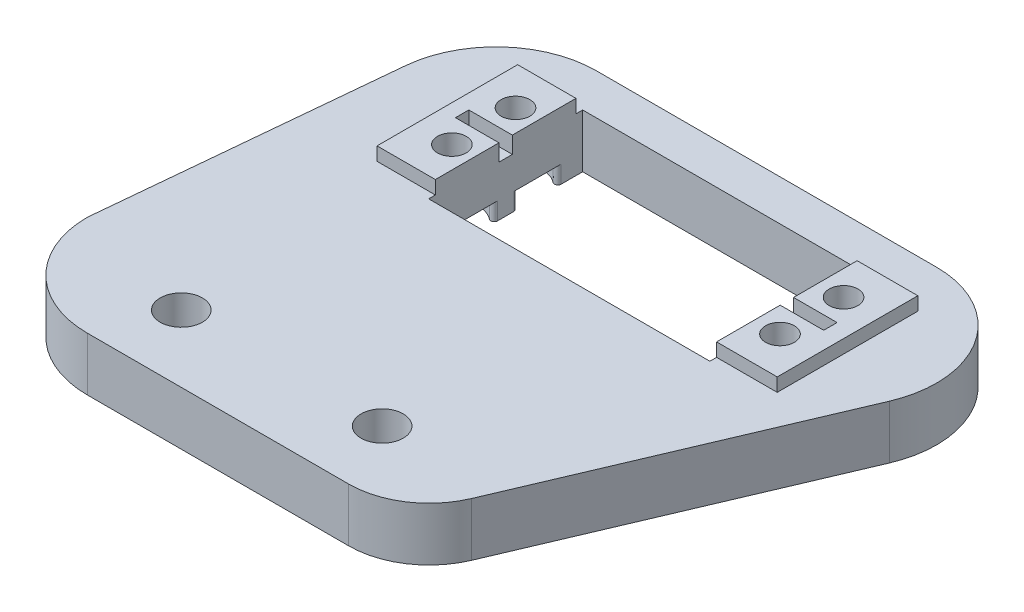
SolidWorks part; units mm, degrees
ref_plane "Front Plane" through (0, 0, 0) normal (0, 0, 1) x (1, 0, 0)
ref_plane "Top Plane" through (0, 0, 0) normal (0, 1, 0) x (1, 0, 0)
ref_plane "Right Plane" through (0, 0, 0) normal (1, 0, 0) x (0, 0, -1)
sketch "Sketch1" plane through (0, 0, 0) normal (0, 1, 0) x (1, 0, 0)
  line L8 (25.9808, 0) -> (65.0096, 0)
  line L9 (10.9808, 15) -> (14.0144, 46.6718)
  line L11 (76.0535, 7.306) -> (90.6678, 41.6903)
  line L12 (90.6678, 41.6903) -> (92.1063, 45.0748)
  line L16 (14.0144, 46.6718) -> (15.1359, 58.3798)
  line L17 (92.1063, 45.0748) -> (94.6596, 51.0821)
  line L19 (80.8548, 71.9495) -> (30.0676, 71.9495)
  arc A7 (25.9808, 0) -> (10.9808, 15) centre (25.9808, 15) cw
  arc A11 (76.0535, 7.306) -> (65.0096, 0) centre (65.0096, 12) cw
  arc A14 (80.8548, 71.9495) -> (94.6596, 51.0821) centre (80.8548, 56.9495) cw
  arc A15 (30.0676, 71.9495) -> (15.1359, 58.3798) centre (30.0676, 56.9495) ccw
  point P8 (0, 0)
  point P11 (0, 0)
  dimension "D1" = 15
extrude "Boss-Extrude1" add sketch "Sketch1" along normal blind 8
sketch "Sketch2" plane through (0, 8, 0) normal (0, 1, 0) x (1, 0, 0)
  line L0 (60, 10) -> (45, 54.3582)
  line L2 (45, 54.3582) -> (39, 54.3582)
  line L5 (45, 54.3582) -> (51, 54.3582)
  circle A2 centre (45, 54.3582) radius 6
  circle A5 centre (30, 10) radius 3.15
  circle A6 centre (60, 10) radius 3.15
  point P3 (57, 10)
  point P10 (57, 10)
extrude "Cut-Extrude1" cut sketch "Sketch2" against normal blind 8
sketch "Sketch3" plane through (0, 8, 0) normal (0, 1, 0) x (1, 0, 0)
  line L0 (25.3837, 64.8582) -> (35.09, 64.8582)
  line L1 (79.81, 54.3582) -> (30.81, 54.3582)
  line L3 (35.09, 64.8582) -> (25.65, 64.8582)
  line L5 (25.3837, 64.8582) -> (25.3837, 43.8582)
  line L6 (25.3837, 43.8582) -> (35.09, 43.8582)
  line L9 (75.15, 43.8582) -> (85.15, 43.8582)
  line L10 (85.15, 43.8582) -> (85.15, 62.71)
  line L12 (85.15, 62.71) -> (85.15, 64.8582)
  line L13 (85.15, 64.8582) -> (75.15, 64.8582)
  line L14 (79.81, 49.6082) -> (79.81, 59.1082)
  line L15 (35.09, 54.3582) -> (35.09, 64.8582)
  line L16 (35.09, 64.8582) -> (35.09, 43.8582)
  line L17 (79.81, 54.3582) -> (75.11, 54.3582)
  line L18 (75.11, 54.3582) -> (75.15, 43.8582)
  line L19 (75.11, 54.3582) -> (75.15, 64.8582)
  line L20 (30.81, 54.3582) -> (30.81, 59.1082)
  line L21 (30.81, 54.3582) -> (30.81, 49.6082)
  circle A4 centre (30.81, 49.6082) radius 2.15
  circle A5 centre (79.81, 49.6082) radius 2.15
  circle A6 centre (79.81, 59.1082) radius 2.15
  circle A7 centre (30.81, 59.1082) radius 2.15
  point P18 (79.81, 54.3582)
extrude "Boss-Extrude3" add sketch "Sketch3" along normal blind 2
sketch "Sketch4" plane through (0, 8, 0) normal (0, 1, 0) x (1, 0, 0)
  line L11 (35.09, 42.8582) -> (34.09, 42.8582)
  line L12 (34.09, 42.8582) -> (34.09, 65.8582)
  line L13 (34.09, 65.8582) -> (76.09, 65.8582)
  line L14 (76.09, 65.8582) -> (76.09, 42.8582)
  line L15 (76.09, 42.8582) -> (34.09, 42.8582)
extrude "Cut-Extrude4" cut sketch "Sketch4" against normal blind 16 and the other way blind 16 contours L12 L13 L14 L15
sketch "Sketch5" plane through (0, 10, 0) normal (0, 1, 0) x (1, 0, 0)
  line L0 (76.09, 54.3582) -> (76.09, 55.3582)
  line L1 (34.09, 64.8582) -> (34.09, 43.8582) construction
  line L2 (27.59, 54.3582) -> (27.59, 55.3582)
  line L3 (27.59, 55.3582) -> (34.09, 55.3582)
  line L4 (34.09, 55.3582) -> (34.09, 53.3582)
  line L5 (34.09, 53.3582) -> (27.59, 53.3582)
  line L6 (27.59, 53.3582) -> (27.59, 54.3582)
  line L7 (76.09, 43.8582) -> (76.09, 64.8582) construction
  line L8 (76.09, 55.3582) -> (82.59, 55.3582)
  line L9 (82.59, 55.3582) -> (82.59, 53.3582)
  line L10 (82.59, 53.3582) -> (76.09, 53.3582)
  line L11 (76.09, 53.3582) -> (76.09, 54.3582)
extrude "Cut-Extrude5" cut sketch "Sketch5" against normal blind 2.5
sketch "Sketch8" plane through (0, 8, 0) normal (0, 1, 0) x (1, 0, 0)
  circle A0 centre (30.81, 49.6082) radius 2.15
  circle A1 centre (30.81, 59.1082) radius 2.15
  circle A2 centre (79.81, 59.1082) radius 2.15
  circle A3 centre (79.81, 49.6082) radius 2.15
extrude "Cut-Extrude8" cut sketch "Sketch8" against normal blind 21.6
sketch "Sketch9" plane through (0, 0, 0) normal (0, -1, 0) x (1, 0, 0)
  circle A0 centre (30.81, -59.1082) radius 4
  circle A1 centre (30.81, -49.6082) radius 4
  circle A2 centre (79.81, -59.1082) radius 4
  circle A3 centre (79.81, -49.6082) radius 4
extrude "Cut-Extrude9" cut sketch "Sketch9" against normal blind 2.6
fillet "Fillet2" radius 0.5 8 edges at (76.09, 1.3, -51.0784) (76.09, 1.3, -48.1379) (76.09, 1.3, -57.6379) (76.09, 1.3, -60.5784) (34.09, 1.3, -51.8976) (34.09, 1.3, -47.3187) (34.09, 1.3, -56.8187) (34.09, 1.3, -61.3976)
